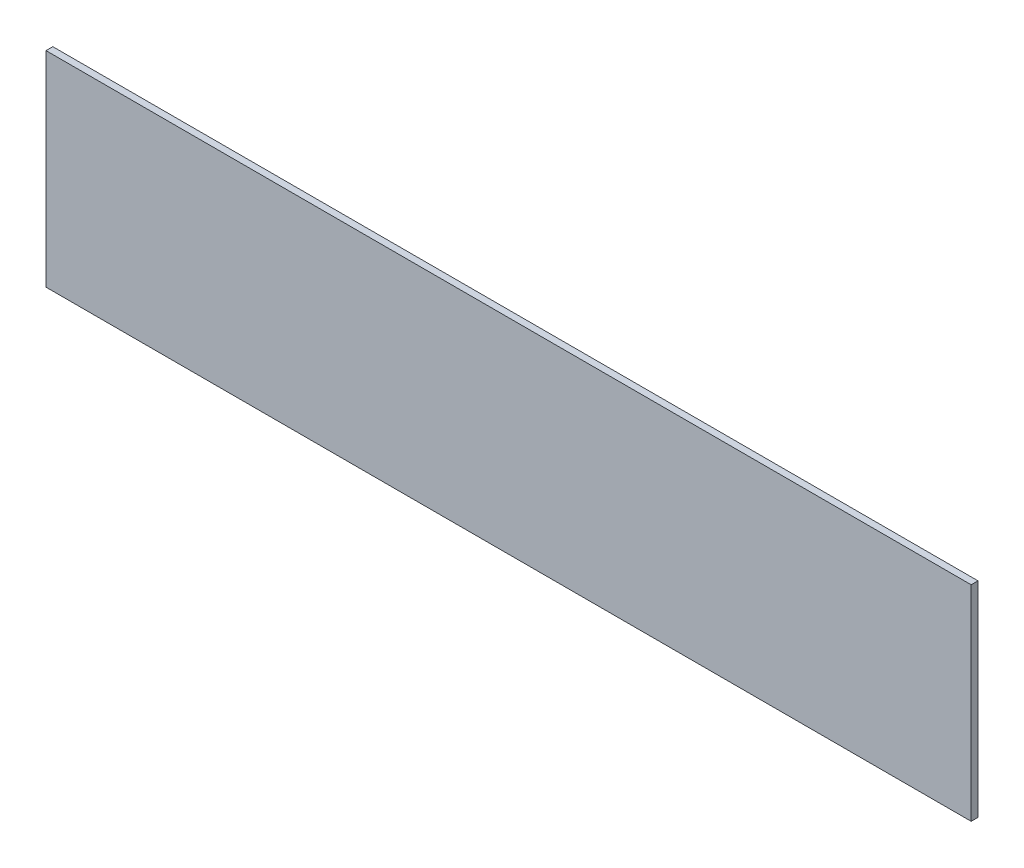
SolidWorks part; units mm, degrees
ref_plane "Front Plane" through (0, 0, 0) normal (0, 0, 1) x (1, 0, 0)
ref_plane "Top Plane" through (0, 0, 0) normal (0, 1, 0) x (1, 0, 0)
ref_plane "Right Plane" through (0, 0, 0) normal (1, 0, 0) x (0, 0, -1)
sketch "Sketch1" plane through (0, 0, 0) normal (0, 0, 1) x (1, 0, 0)
  line L1 (101.6, -22.5) -> (-101.6, -22.5)
  line L2 (101.6, -22.5) -> (101.6, 22.5)
  line L3 (101.6, 22.5) -> (-101.6, 22.5)
  line L4 (-101.6, -22.5) -> (-101.6, 22.5)
  line L5 (101.6, -22.5) -> (-101.6, 22.5) construction
  line L6 (101.6, 22.5) -> (-101.6, -22.5) construction
  point P0 (0, 0)
extrude "Boss-Extrude1" add sketch "Sketch1" along normal blind 1.5
